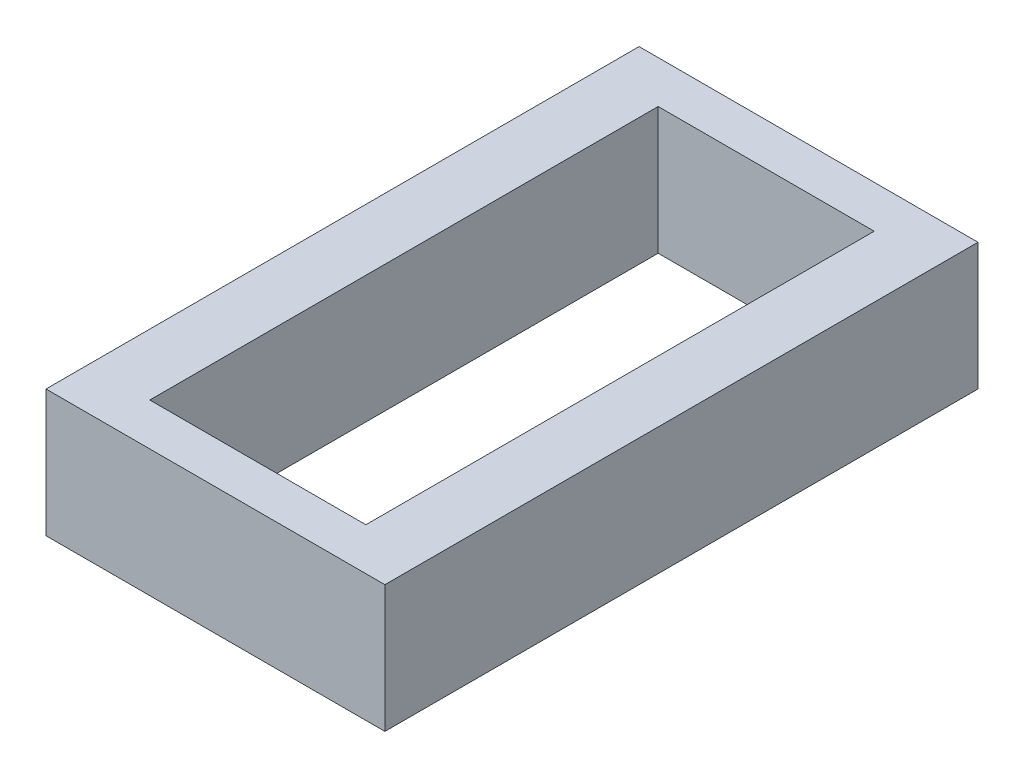
SolidWorks part; units mm, degrees
ref_plane "Front Plane" through (0, 0, 0) normal (0, 0, 1) x (1, 0, 0)
ref_plane "Top Plane" through (0, 0, 0) normal (0, 1, 0) x (1, 0, 0)
ref_plane "Right Plane" through (0, 0, 0) normal (1, 0, 0) x (0, 0, -1)
sketch "Sketch1" plane through (0, 0, 0) normal (0, 1, 0) x (1, 0, 0)
  line L1 (-4, 7) -> (4, 7)
  line L2 (-4, 7) -> (-4, -7)
  line L3 (-4, -7) -> (4, -7)
  line L4 (4, 7) -> (4, -7)
  line L5 (-4, 7) -> (4, -7) construction
  line L6 (-4, -7) -> (4, 7) construction
  line L7 (-2.55, 6) -> (2.55, 6)
  line L8 (-2.55, 6) -> (-2.55, -6)
  line L9 (-2.55, -6) -> (2.55, -6)
  line L10 (2.55, 6) -> (2.55, -6)
  line L11 (-2.55, 6) -> (2.55, -6) construction
  line L12 (-2.55, -6) -> (2.55, 6) construction
  point P0 (0, 0)
  point P6 (0, 0)
  dimension "D1" = 8
  dimension "D2" = 14
  dimension "D3" = 5.1
  dimension "D4" = 12
extrude "Boss-Extrude1" add sketch "Sketch1" along normal blind 3
